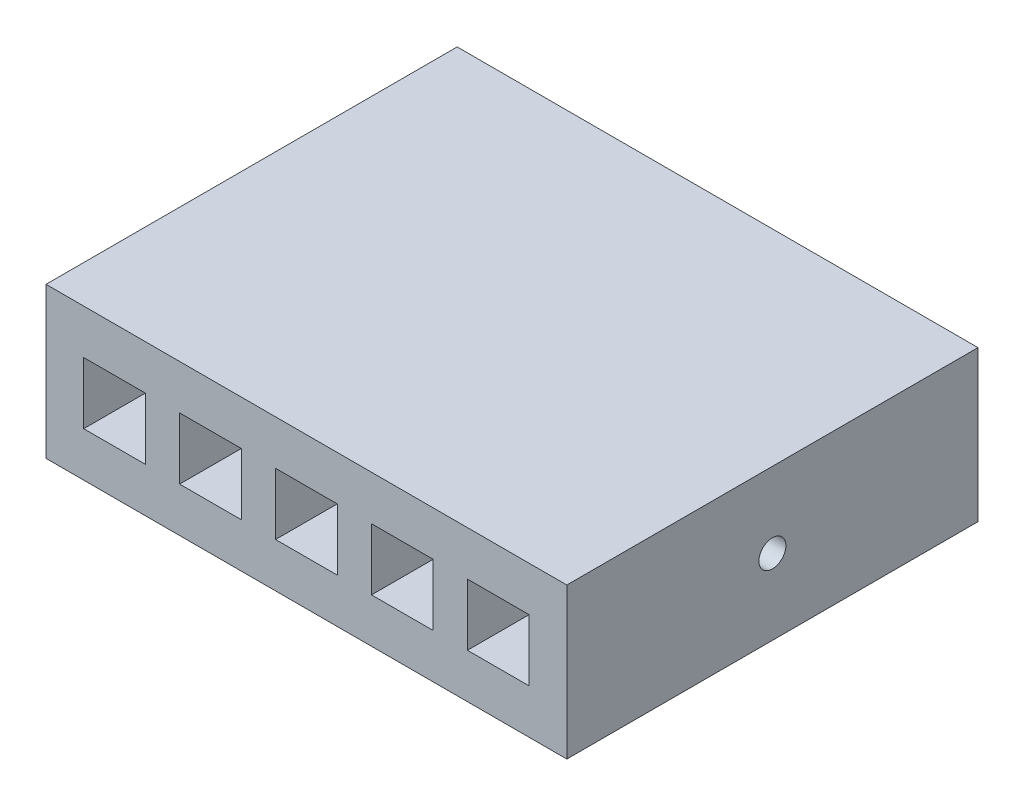
SolidWorks part; units mm, degrees
ref_plane "Front Plane" through (0, 0, 0) normal (0, 0, 1) x (1, 0, 0)
ref_plane "Top Plane" through (0, 0, 0) normal (0, 1, 0) x (1, 0, 0)
ref_plane "Right Plane" through (0, 0, 0) normal (1, 0, 0) x (0, 0, -1)
sketch "Sketch1" plane through (0, 0, 0) normal (0, 1, 0) x (1, 0, 0)
  line L1 (0, 0) -> (96.52, 0)
  line L2 (0, 0) -> (0, 76.2)
  line L3 (0, 76.2) -> (96.52, 76.2)
  line L4 (96.52, 0) -> (96.52, 76.2)
  dimension "D1" = 76.2
  dimension "D2" = 96.52
extrude "Boss-Extrude1" add sketch "Sketch1" along normal blind 27.94
sketch "Sketch2" plane through (0, 0, 0) normal (0, 0, 1) x (1, 0, 0)
  line L0 (18.415, 19.685) -> (24.765, 19.685) construction
  line L1 (6.985, 19.685) -> (18.415, 19.685)
  line L2 (6.985, 19.685) -> (6.985, 8.255)
  line L3 (6.985, 8.255) -> (18.415, 8.255)
  line L4 (18.415, 19.685) -> (18.415, 8.255)
  line L5 (24.765, 19.685) -> (36.195, 19.685)
  line L6 (24.765, 19.685) -> (24.765, 8.255)
  line L7 (24.765, 8.255) -> (36.195, 8.255)
  line L8 (36.195, 19.685) -> (36.195, 8.255)
  line L9 (42.545, 19.685) -> (53.975, 19.685)
  line L10 (42.545, 19.685) -> (42.545, 8.255)
  line L11 (42.545, 8.255) -> (53.975, 8.255)
  line L12 (53.975, 19.685) -> (53.975, 8.255)
  line L13 (60.325, 19.685) -> (71.755, 19.685)
  line L14 (60.325, 19.685) -> (60.325, 8.255)
  line L15 (60.325, 8.255) -> (71.755, 8.255)
  line L16 (71.755, 19.685) -> (71.755, 8.255)
  line L17 (78.105, 19.685) -> (89.535, 19.685)
  line L18 (78.105, 19.685) -> (78.105, 8.255)
  line L19 (78.105, 8.255) -> (89.535, 8.255)
  line L20 (89.535, 19.685) -> (89.535, 8.255)
  line L21 (36.195, 19.685) -> (42.545, 19.685) construction
  line L22 (53.975, 19.685) -> (60.325, 19.685) construction
  line L23 (71.755, 19.685) -> (78.105, 19.685) construction
  line L24 (6.985, 19.685) -> (0, 19.685) construction
  line L25 (0, 27.94) -> (0, 0) construction
  line L26 (89.535, 19.685) -> (89.535, 27.94) construction
  line L27 (0, 27.94) -> (96.52, 27.94) construction
  line L28 (96.52, 27.94) -> (96.52, 0) construction
  line L29 (96.52, 19.685) -> (89.535, 19.685) construction
  line L32 (0, 0) -> (96.52, 0) construction
  line L33 (89.535, 0) -> (89.535, 8.255) construction
  dimension "D1" = 11.43
  dimension "D2" = 6.35
extrude "Cut-Extrude1" cut sketch "Sketch2" against normal blind 11.43 contours L4 L1 L2 L3 | L8 L5 L6 L7 | L12 L9 L10 L11 | L16 L13 L14 L15 | L20 L17 L18 L19
sketch "Sketch3" plane through (96.52, 0, 0) normal (1, 0, 0) x (0, 0, -1)
  line L0 (38.1, 13.97) -> (38.1, 0) construction
  line L1 (0, 0) -> (76.2, 0) construction
  line L3 (0, 27.94) -> (0, 0) construction
  line L4 (0, 13.97) -> (38.1, 13.97) construction
  circle A0 centre (38.1, 13.97) radius 2.5
  dimension "D1" = 5
extrude "Cut-Extrude2" cut sketch "Sketch3" against normal blind 12.7
